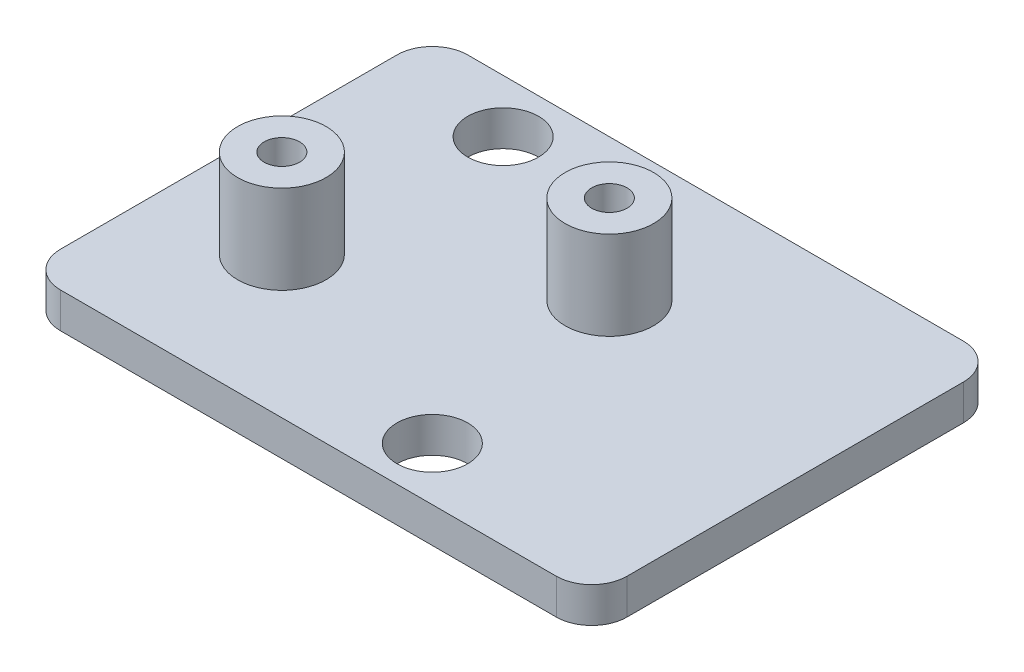
SolidWorks part; units mm, degrees
material "ABS"
ref_plane "Спереди" through (0, 0, 0) normal (0, 0, 1) x (1, 0, 0)
ref_plane "Сверху" through (0, 0, 0) normal (0, 1, 0) x (1, 0, 0)
ref_plane "Справа" through (0, 0, 0) normal (1, 0, 0) x (0, 0, -1)
sketch "Эскиз1" plane through (0, 0, 0) normal (0, 1, 0) x (1, 0, 0)
  line L1 (0, 0) -> (32, 0)
  line L2 (0, 0) -> (0, -23)
  line L3 (0, -23) -> (32, -23)
  line L4 (32, 0) -> (32, -23)
  dimension "D1" = 32
  dimension "D2" = 23
extrude "Бобышка-Вытянуть1" add sketch "Эскиз1" along normal blind 2
sketch "Эскиз4" plane through (0, 2, 0) normal (0, 1, 0) x (1, 0, 0)
  line L0 (0, 0) -> (32, 0) construction
  line L1 (0, -23) -> (32, -23) construction
  line L2 (0, 0) -> (0, -23) construction
  line L3 (32, 0) -> (32, -23) construction
  circle A0 centre (18, -8) radius 2.5
  circle A1 centre (6.5, -15) radius 2.5
  dimension "D1" = 8
  dimension "D2" = 8
  dimension "D3" = 6.5
  dimension "D4" = 14
  dimension "D5" = 5
  dimension "D6" = 5
extrude "Бобышка-Вытянуть2" add sketch "Эскиз4" along normal blind 5
sketch "Эскиз5" plane through (0, 7, 0) normal (0, 1, 0) x (1, 0, 0)
  circle A0 centre (6.5, -15) radius 1
  circle A1 centre (18, -8) radius 1
  dimension "D1" = 2
  dimension "D2" = 2
extrude "Вырез-Вытянуть1" cut sketch "Эскиз5" against normal through all
sketch "Эскиз7" plane through (0, 2, 0) normal (0, 1, 0) x (1, 0, 0)
  line L0 (0, 0) -> (32, 0) construction
  line L1 (0, -23) -> (32, -23) construction
  line L2 (32, 0) -> (32, -23) construction
  line L3 (0, 0) -> (0, -23) construction
  circle A0 centre (7, -3) radius 2
  circle A1 centre (20, -20) radius 2
  dimension "D1" = 3
  dimension "D2" = 4
  dimension "D3" = 3
  dimension "D4" = 4
  dimension "D5" = 12
  dimension "D6" = 7
extrude "Вырез-Вытянуть2" cut sketch "Эскиз7" against normal through all
fillet "Скругление1" radius 2 1 edges at (0, 1, 0)
fillet "Скругление2" radius 2 1 edges at (0, 1, 23)
fillet "Скругление3" radius 2 1 edges at (32, 1, 23)
fillet "Скругление4" radius 2 1 edges at (32, 1, 0)
